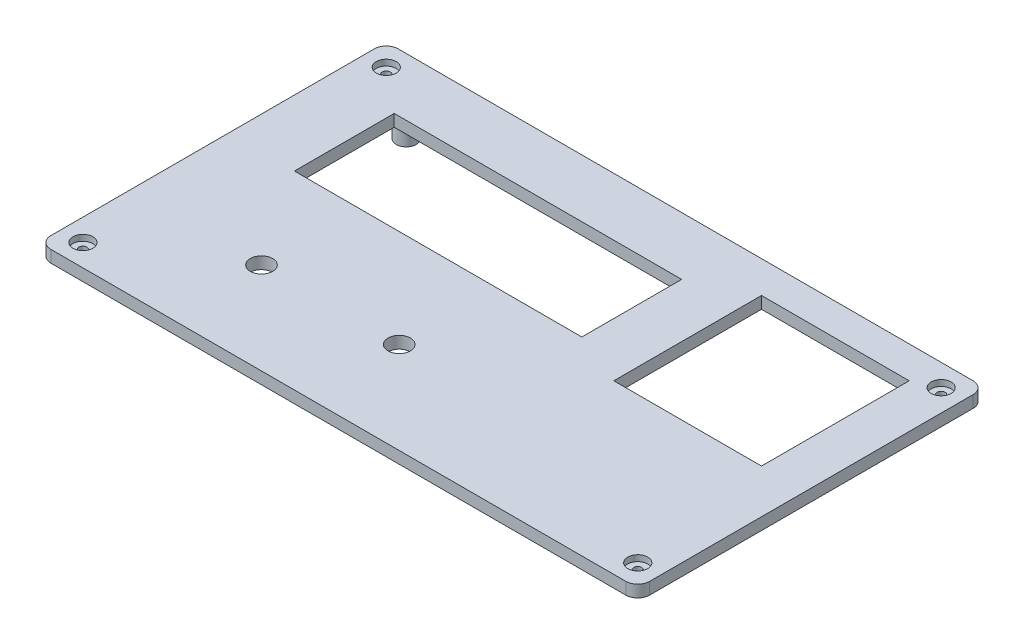
SolidWorks part; units mm, degrees
ref_plane "Front Plane" through (0, 0, 0) normal (0, 0, 1) x (1, 0, 0)
ref_plane "Top Plane" through (0, 0, 0) normal (0, 1, 0) x (1, 0, 0)
ref_plane "Right Plane" through (0, 0, 0) normal (1, 0, 0) x (0, 0, -1)
sketch "Cover_frame" plane through (0, 0, 0) normal (0, 1, 0) x (1, 0, 0)
  line L1 (0, 0) -> (150, 0)
  line L2 (0, 0) -> (0, 87)
  line L3 (0, 87) -> (150, 87)
  line L4 (150, 0) -> (150, 87)
  dimension "D1" = 87
  dimension "D2" = 150
extrude "cover_thickness" add sketch "Cover_frame" along normal blind 3
sketch "cover_items_mouting_holes" plane through (0, 0, 0) normal (0, -1, 0) x (1, 0, 0)
  line L0 (13, -87) -> (13, -79) construction
  line L1 (150, -87) -> (0, -87) construction
  line L2 (0, 0) -> (150, 0) construction
  line L3 (18, -87) -> (18, -79) construction
  line L4 (0, -87) -> (0, 0) construction
  line L5 (0, -79) -> (13, -79) construction
  line L6 (150, 0) -> (150, -87) construction
  line L7 (18, -74) -> (88, -74) construction
  line L8 (87, -38) -> (87, -33) construction
  line L9 (0, -43) -> (13, -43) construction
  line L10 (0, -48) -> (13, -48) construction
  line L11 (93, -74) -> (93, -48) construction
  line L12 (88, -74) -> (88, -48) construction
  line L17 (18, -74) -> (18, -48) construction
  line L30 (18, -79) -> (88, -79) construction
  line L31 (13, -74) -> (13, -48) construction
  line L32 (18, -43) -> (18, 0) construction
  line L33 (18, -48) -> (88, -48) construction
  line L34 (13, -43) -> (13, 0) construction
  line L35 (0, -38) -> (150, -38) construction
  line L36 (93, -74) -> (150, -74) construction
  line L37 (0, -8) -> (150, -8) construction
  line L38 (93, -48) -> (150, -48) construction
  line L39 (13, -33) -> (87, -33) construction
  line L40 (13, -13) -> (87, -13) construction
  line L41 (82, -38) -> (82, -8) construction
  line L42 (87, -13) -> (87, -8) construction
  circle A0 centre (15.5, -76.5) radius 1
  circle A1 centre (15.5, -76.5) radius 2.5
  circle A2 centre (15.5, -45.5) radius 1
  circle A3 centre (15.5, -45.5) radius 1.75
  circle A4 centre (90.5, -76.5) radius 1
  circle A5 centre (90.5, -76.5) radius 2.5
  circle A6 centre (90.5, -45.5) radius 1
  circle A7 centre (90.5, -45.5) radius 2.5
  circle A8 centre (15.5, -35.5) radius 1
  circle A9 centre (15.5, -35.5) radius 2.5
  circle A10 centre (15.5, -10.5) radius 1
  circle A11 centre (15.5, -10.5) radius 2.5
  circle A12 centre (84.5, -35.5) radius 1
  circle A13 centre (84.5, -35.5) radius 2.5
  circle A14 centre (84.5, -10.5) radius 1
  circle A15 centre (84.5, -10.5) radius 2.5
  dimension "D9" = 2
  dimension "D10" = 2
  dimension "D11" = 2
  dimension "D12" = 30
  dimension "D7" = 2
  dimension "D17" = 2
  dimension "D18" = 2.5
  dimension "D19" = 2
  dimension "D20" = 2.5
  dimension "D21" = 2.5
  dimension "D22" = 2
  dimension "D23" = 2
  dimension "D24" = 3.5
  dimension "D1" = 13
  dimension "D2" = 5
  dimension "D3" = 8
  dimension "D4" = 5
  dimension "D5" = 36
  dimension "D6" = 5
  dimension "D8" = 5
  dimension "D13" = 5
  dimension "D14" = 5
  dimension "D15" = 74
  dimension "D16" = 5
extrude "cover_items_holes" add sketch "cover_items_mouting_holes" along normal blind 5
sketch "Cover_screw_holes" plane through (0, 3, 0) normal (0, 1, 0) x (1, 0, 0)
  line L0 (0, 84) -> (150, 84) construction
  line L1 (0, 87) -> (0, 0) construction
  line L2 (150, 0) -> (150, 87) construction
  line L3 (0, 3) -> (150, 3) construction
  line L4 (3, 87) -> (3, 0) construction
  line L5 (150, 87) -> (0, 87) construction
  line L6 (0, 0) -> (150, 0) construction
  line L7 (147, 87) -> (147, 0) construction
  line L8 (8, 84) -> (8, 3) construction
  line L9 (142, 84) -> (142, 3) construction
  line L10 (3, 79) -> (147, 79) construction
  line L11 (3, 8) -> (147, 8) construction
  circle A0 centre (5.5, 81.5) radius 1
  circle A1 centre (5.5, 5.5) radius 1
  dimension "D9" = 2
  dimension "D10" = 2.5
  dimension "D11" = 2.5
  dimension "D12" = 2
  dimension "D13" = 2.5
  dimension "D1" = 3
  dimension "D2" = 3
  dimension "D3" = 3
  dimension "D4" = 3
  dimension "D5" = 5
  dimension "D6" = 5
  dimension "D7" = 5
  dimension "D8" = 5
extrude "cover_screw" cut sketch "Cover_screw_holes" against normal through all
ref_plane "Plane_cover_screw_holes" through (75, 0, 0) normal (-1, 0, 0) x (0, 0, 1)
mirror "Mirror2" about plane through (75, 0, 0) normal (-1, 0, 0) of "cover_screw"
fillet "cover_edges" radius 3 4 edges at (0, 1.5, -87) (150, 1.5, -87) (150, 1.5, 0) (0, 1.5, 0)
sketch "Sketch10" plane through (0, 3, 0) normal (0, 1, 0) x (1, 0, 0)
  line L0 (147, 87) -> (3, 87) construction
  line L1 (102, 79) -> (139, 79)
  line L2 (102, 79) -> (102, 42)
  line L3 (102, 42) -> (139, 42)
  line L4 (139, 79) -> (139, 42)
  line L5 (150, 3) -> (150, 84) construction
  dimension "D1" = 37
  dimension "D2" = 8
  dimension "D3" = 37
  dimension "D4" = 11
extrude "Load_outlet" cut sketch "Sketch10" against normal through all
sketch "Sketch11" plane through (0, 0, 0) normal (0, -1, 0) x (1, 0, 0)
  line L0 (84.5, -35.5) -> (15.5, -35.5) construction
  line L1 (15.5, -35.5) -> (15.5, -10.5) construction
  line L2 (15.5, -10.5) -> (84.5, -10.5) construction
  line L3 (84.5, -10.5) -> (84.5, -35.5) construction
  line L4 (50, -35.5) -> (50, -10.5) construction
  line L5 (67.25, -35.5) -> (67.25, -10.5) construction
  line L6 (32.75, -35.5) -> (32.75, -10.5) construction
  line L7 (84.5, -23) -> (15.5, -23) construction
  circle A0 centre (67.25, -23) radius 2.8
  circle A1 centre (32.75, -23) radius 2.8
  dimension "D3" = 5.6
  dimension "D4" = 5.6
  dimension "D1" = 17.25
  dimension "D2" = 17.25
extrude "Indicator_leds" cut sketch "Sketch11" against normal through all
sketch "Sketch12" plane through (0, 0, 0) normal (0, -1, 0) x (1, 0, 0)
  line L0 (90.5, -76.5) -> (15.5, -76.5) construction
  line L1 (15.5, -76.5) -> (15.5, -45.5) construction
  line L2 (15.5, -45.5) -> (90.5, -45.5) construction
  line L3 (90.5, -45.5) -> (90.5, -76.5) construction
  line L4 (53, -76.5) -> (53, -45.5) construction
  line L6 (88.5, -72.5) -> (16.5, -72.5)
  line L7 (88.5, -72.5) -> (88.5, -47.5)
  line L8 (88.5, -47.5) -> (16.5, -47.5)
  line L9 (16.5, -72.5) -> (16.5, -47.5)
  dimension "D1" = 25
  dimension "D2" = 72
  dimension "D3" = 4
  dimension "D4" = 2
extrude "LCD" cut sketch "Sketch12" against normal through all
sketch "Sketch13" plane through (0, 3, 0) normal (0, 1, 0) x (1, 0, 0)
  circle A0 centre (5.5, 81.5) radius 2.5
  circle A1 centre (5.5, 5.5) radius 2.5
  dimension "D1" = 5
  dimension "D2" = 5
extrude "cover_screw_countersunk" cut sketch "Sketch13" against normal blind 1.5
mirror "Mirror3" about plane through (75, 0, 0) normal (-1, 0, 0) of "cover_screw_countersunk"
